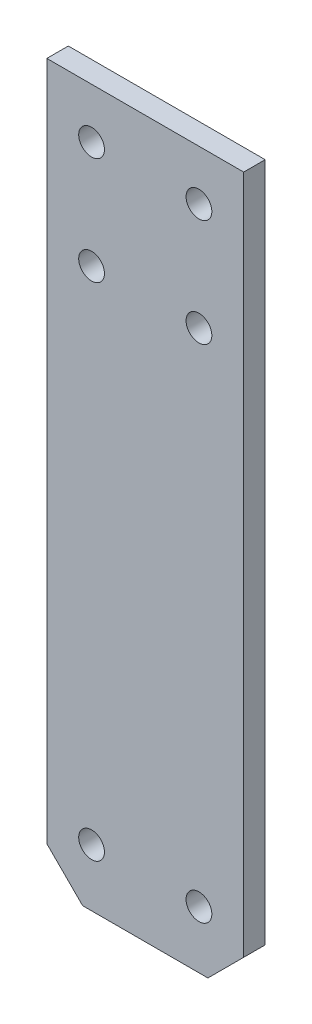
SolidWorks part; units mm, degrees
ref_plane "Front Plane" through (0, 0, 0) normal (0, 0, 1) x (1, 0, 0)
ref_plane "Top Plane" through (0, 0, 0) normal (0, 1, 0) x (1, 0, 0)
ref_plane "Right Plane" through (0, 0, 0) normal (1, 0, 0) x (0, 0, -1)
sketch "Sketch1" plane through (0, 0, 0) normal (0, 0, 1) x (1, 0, 0)
  line L1 (-13.75, -50) -> (13.75, -50)
  line L2 (-13.75, -50) -> (-13.75, 50)
  line L3 (-13.75, 50) -> (13.75, 50)
  line L4 (13.75, -50) -> (13.75, 50)
  line L5 (-13.75, -50) -> (13.75, 50) construction
  line L6 (-13.75, 50) -> (13.75, -50) construction
  point P0 (0, 0)
  dimension "D1" = 27.5
  dimension "D2" = 100
extrude "Boss-Extrude1" add sketch "Sketch1" along normal blind 3
sketch "Sketch3" plane through (0, 0, 3) normal (0, 0, 1) x (1, 0, 0)
  line L0 (13.75, -50) -> (13.75, 50) construction
  line L1 (13.75, 50) -> (-13.75, 50) construction
  line L2 (-13.75, -50) -> (13.75, -50) construction
  point P0 (-7.5, 43)
  point P1 (7.5, 43)
  point P2 (7.5, 28)
  point P3 (-7.5, 28)
  point P9 (-7.5, -42)
  point P10 (7.5, -42)
  dimension "D1" = 6.25
  dimension "D2" = 21.25
  dimension "D3" = 7
  dimension "D4" = 22
  dimension "D5" = 15
  dimension "D6" = 8
hole_wizard "M3 Clearance Hole1" positions "Sketch4" profile "Sketch5" hole size "M3" standard "ISO"
sketch "Sketch4" plane through (0, 0, 3) normal (0, 0, 1) x (1, 0, 0)
  point P0 (-7.5, 43)
  point P3 (7.5, 43)
  point P6 (7.5, 28)
  point P9 (-7.5, 28)
  point P13 (-7.5, -42)
  point P16 (7.5, -42)
sketch "Sketch5" plane through (-7.5, 43, 3) normal (1, 0, 0) x (0, -1, 0)
  line L0 (0, 0) -> (0, 31.0815)
  line L1 (0, 31.0815) -> (1.8, 30)
  line L2 (1.8, 30) -> (1.8, 0)
  line L5 (1.8, 0) -> (0, 0)
  line L10 (0, 31.0815) -> (-1.8, 30) construction
  line L11 (0, -6.35) -> (0, 107.95) construction
  dimension "Hole Dia." = 3.6
  dimension "Hole Depth" = 30
  dimension "Drill Angle" = 118
chamfer "Chamfer1" distance 5 angle 45 2 edges at (13.75, -50, 1.5) (-13.75, -50, 1.5)
